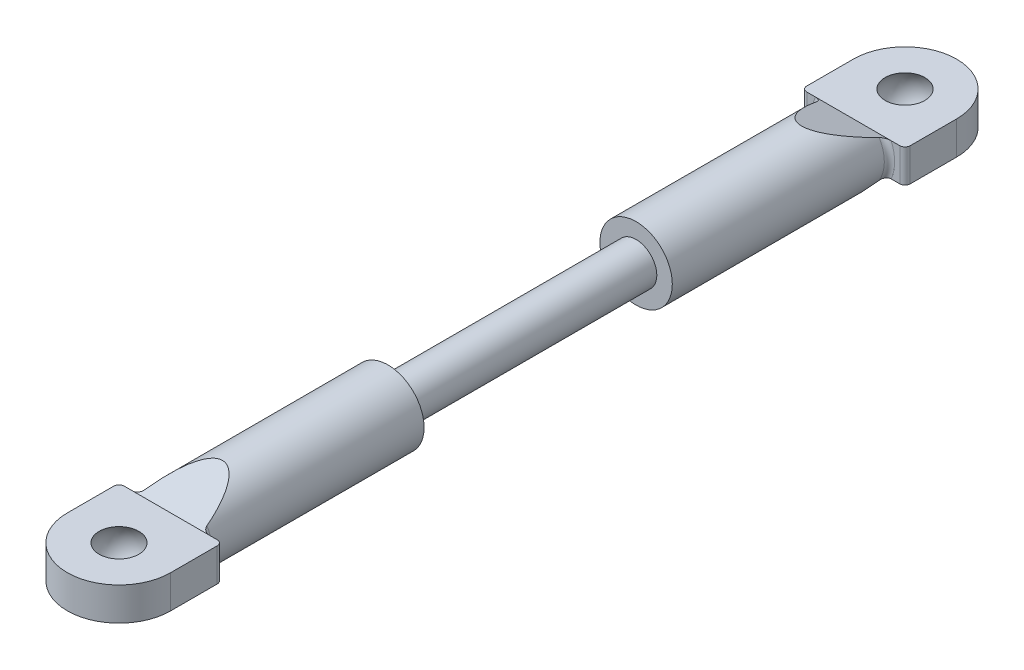
SolidWorks part; units mm, degrees
ref_plane "Front Plane" through (0, 0, 0) normal (0, 0, 1) x (1, 0, 0)
ref_plane "Top Plane" through (0, 0, 0) normal (0, 1, 0) x (1, 0, 0)
ref_plane "Right Plane" through (0, 0, 0) normal (1, 0, 0) x (0, 0, -1)
sketch "Sketch1" plane through (0, 0, 0) normal (0, 0, 1) x (1, 0, 0)
  circle A0 centre (0, 0) radius 2
  dimension "D1" = 4
extrude "Screw Section" add sketch "Sketch1" along normal blind 12 contours A0
sketch "Sketch2" plane through (0, 0, 12) normal (0, 0, 1) x (1, 0, 0)
  circle A0 centre (0, 0) radius 3.5
  dimension "D1" = 7
extrude "Bar Section" add sketch "Sketch2" along normal blind 21
sketch "Sketch3" plane through (0, 0, 0) normal (0, 1, 0) x (1, 0, 0)
  line L0 (5, -33) -> (-5, -33)
  line L1 (-5, -33) -> (-5, -38)
  line L2 (5, -33) -> (5, -38)
  line L3 (-3.5, -33) -> (3.5, -33) construction
  arc A0 (-5, -38) -> (5, -38) centre (0, -38) ccw
  point P4 (0, -43)
  dimension "D1" = 5
  dimension "D2" = 10
  dimension "D3" = 10
extrude "Mount Section" add sketch "Sketch3" along normal mid plane 3.2
sketch "Sketch4" plane through (0, 0, 0) normal (1, 0, 0) x (0, 0, -1)
  line L0 (-28, -3.5) -> (-33, -1.6)
  line L1 (-33, -3.5) -> (-12, -3.5) construction
  line L2 (-33, -1.6) -> (-33, -3.5)
  line L3 (-33, -1.6) -> (-33, -3.5) construction
  line L4 (-33, -3.5) -> (-28, -3.5)
  line L5 (-28, 3.5) -> (-33, 1.6)
  line L6 (-33, 3.5) -> (-33, 1.6) construction
  line L7 (-33, 3.5) -> (-28, 3.5)
  line L9 (-33, 1.6) -> (-33, 3.5)
  dimension "D1" = 5
  dimension "D2" = 1.9
extrude "Bar Taper" cut sketch "Sketch4" against normal through all both and the other way through all
fillet "Mount Fillet" radius 0.5 4 edges at (-5, 0, 33) (3.5, 0, 33) (-3.5, 0, 33) (5, 0, 33)
sketch "Sketch6" plane through (0, 0, 0) normal (1, 0, 0) x (0, 0, -1)
  line L0 (-38, 1.6) -> (-38, -1.6) construction
  line L1 (-43, -1.6) -> (-38, -1.6) construction
  line L2 (-38, 1.6) -> (-43, 1.6) construction
  line L4 (-39.9209, -1.6) -> (-38, -1.6)
  line L5 (-38, -1.6) -> (-38, 1.6)
  line L6 (-38, 1.6) -> (-39.9209, 1.6)
  arc A0 (-39.9209, -1.6) -> (-39.9209, 1.6) centre (-38, 0) cw
  dimension "D1" = 2.5
revolve "Ball Hole" cut sketch "Sketch6" angle 360 about L5
mirror "Mirror" about plane through (0, 0, 0) normal (0, 0, 1) of "Ball Hole", "Bar Section", "Bar Taper", "Mount Section", "Mount Fillet", "Screw Section"
ref_point "Point1"
ref_point "Point2"
